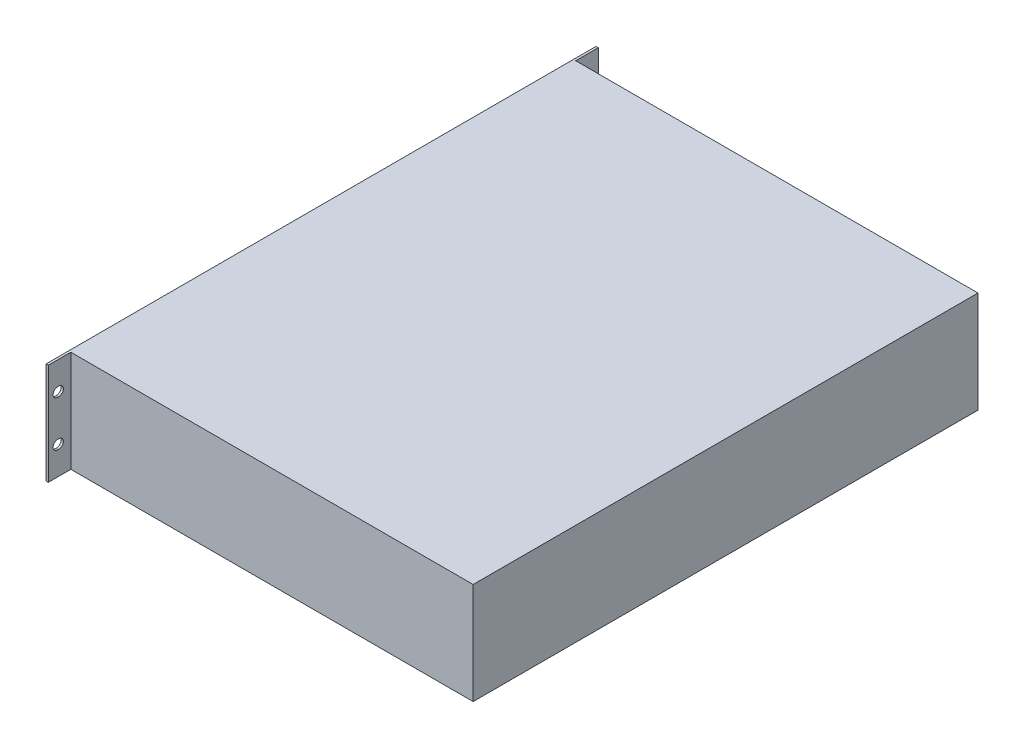
SolidWorks part; units mm, degrees
ref_plane "Front" through (0, 0, 0) normal (0, 0, 1) x (1, 0, 0)
ref_plane "Top" through (0, 0, 0) normal (0, 1, 0) x (1, 0, 0)
ref_plane "Right" through (0, 0, 0) normal (1, 0, 0) x (0, 0, -1)
sketch "Croquis1" plane through (0, 0, 0) normal (0, 1, 0) x (1, 0, 0)
  line L1 (-177.5, 221.5) -> (177.5, 221.5)
  line L2 (-177.5, 221.5) -> (-177.5, -221.5)
  line L3 (-177.5, -221.5) -> (177.5, -221.5)
  line L4 (177.5, 221.5) -> (177.5, -221.5)
  line L5 (-177.5, 221.5) -> (177.5, -221.5) construction
  line L6 (-177.5, -221.5) -> (177.5, 221.5) construction
  point P0 (0, 0)
  dimension "D1" = 443
  dimension "D2" = 355
extrude "Saliente-Extruir1" add sketch "Croquis1" along normal blind 89
sketch "Croquis2" plane through (-177.5, 0, 0) normal (-1, 0, 0) x (0, 0, 1)
  line L0 (2.9991, 44.5) -> (-49997.0009, 44.5) construction
  line L1 (-241.3, 0) -> (241.3, 0)
  line L2 (-241.3, 0) -> (-241.3, 89)
  line L3 (-241.3, 89) -> (241.3, 89)
  line L4 (241.3, 0) -> (241.3, 89)
  line L5 (-241.3, 0) -> (241.3, 89) construction
  line L6 (-241.3, 89) -> (241.3, 0) construction
  line L7 (0, 50) -> (0, 50050) construction
  line L8 (-233.06, 64.5) -> (-232.06, 64.5) construction
  line L9 (-233.06, 68.5) -> (-232.06, 68.5)
  line L10 (-233.06, 60.5) -> (-232.06, 60.5)
  line L11 (-233.06, 24.5) -> (-232.06, 24.5) construction
  line L12 (-233.06, 20.5) -> (-232.06, 20.5)
  line L13 (-233.06, 28.5) -> (-232.06, 28.5)
  line L14 (233.06, 64.5) -> (232.06, 64.5) construction
  line L15 (233.06, 68.5) -> (232.06, 68.5)
  line L16 (233.06, 60.5) -> (232.06, 60.5)
  line L17 (233.06, 24.5) -> (232.06, 24.5) construction
  line L18 (233.06, 20.5) -> (232.06, 20.5)
  line L19 (233.06, 28.5) -> (232.06, 28.5)
  arc A0 (-233.06, 68.5) -> (-233.06, 60.5) centre (-233.06, 64.5) ccw
  arc A1 (-232.06, 60.5) -> (-232.06, 68.5) centre (-232.06, 64.5) ccw
  arc A2 (-233.06, 20.5) -> (-233.06, 28.5) centre (-233.06, 24.5) cw
  arc A3 (-232.06, 28.5) -> (-232.06, 20.5) centre (-232.06, 24.5) cw
  arc A4 (233.06, 68.5) -> (233.06, 60.5) centre (233.06, 64.5) cw
  arc A5 (232.06, 60.5) -> (232.06, 68.5) centre (232.06, 64.5) cw
  arc A6 (233.06, 20.5) -> (233.06, 28.5) centre (233.06, 24.5) ccw
  arc A7 (232.06, 28.5) -> (232.06, 20.5) centre (232.06, 24.5) ccw
  point P4 (0, 44.5)
  point P14 (-232.56, 64.5)
  point P21 (-232.56, 24.5)
  point P28 (232.56, 64.5)
  point P35 (232.56, 24.5)
  dimension "D3" = 4
  dimension "D1" = 482.6
  dimension "D2" = 40
  dimension "D4" = 1
  dimension "D5" = 465.12
extrude "Saliente-Extruir2" add sketch "Croquis2" against normal blind 2
